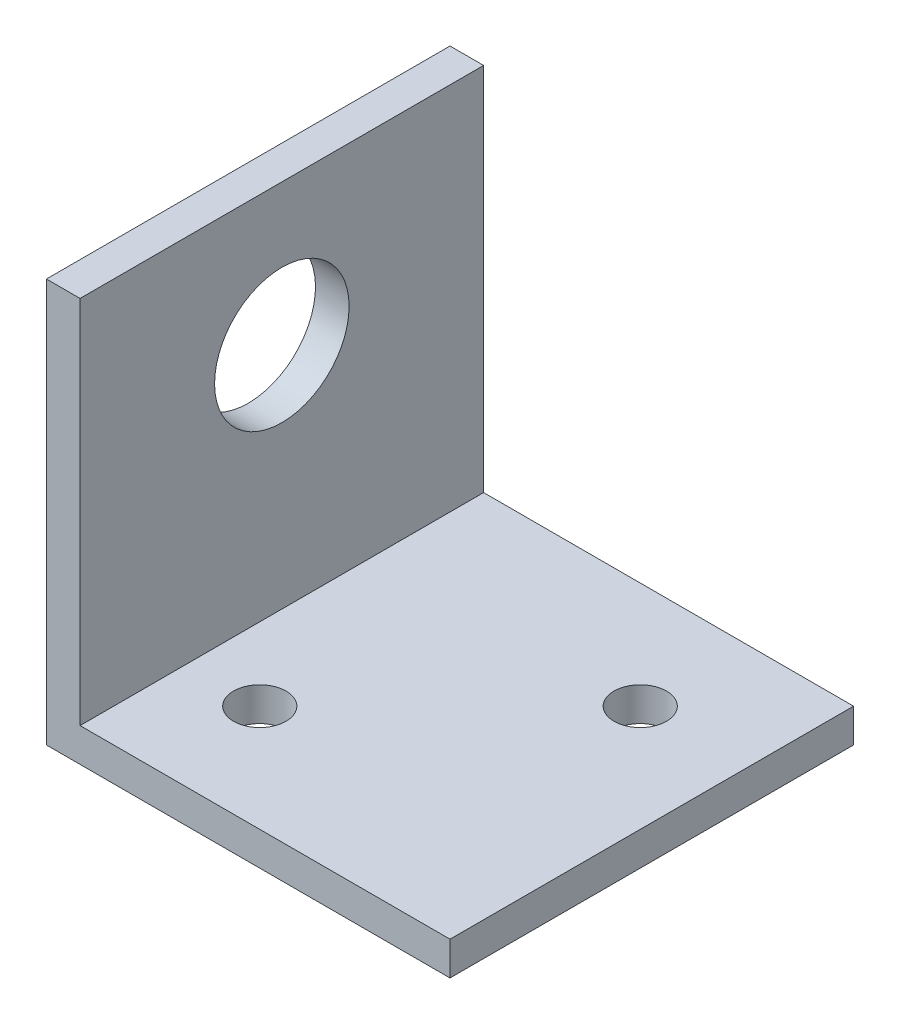
SolidWorks part; units mm, degrees
ref_plane "Front Plane" through (0, 0, 0) normal (0, 0, 1) x (1, 0, 0)
ref_plane "Top Plane" through (0, 0, 0) normal (0, 1, 0) x (1, 0, 0)
ref_plane "Right Plane" through (0, 0, 0) normal (1, 0, 0) x (0, 0, -1)
sketch "Sketch1" plane through (0, 0, 0) normal (0, 0, 1) x (1, 0, 0)
  line L0 (0, 38.1) -> (0, 0)
  line L1 (0, 0) -> (38.1, 0)
  dimension "D1" = 38.1
extrude "Extrude-Thin1" add sketch "Sketch1" along normal blind 38.1 thin thin type one direction reverse wall 3.175
sketch "Sketch2" plane through (0, 0, 0) normal (-1, 0, 0) x (0, 0, 1)
  line L0 (19.05, 0) -> (19.05, 38.1) construction
  line L1 (38.1, 0) -> (0, 0) construction
  line L2 (38.1, 38.1) -> (0, 38.1) construction
  circle A0 centre (19.05, 24.765) radius 6.35
  dimension "D1" = 12.7
  dimension "D2" = 13.335
extrude "Cut-Extrude1" cut sketch "Sketch2" against normal through all
sketch "Sketch3" plane through (0, 0, 0) normal (0, -1, 0) x (1, 0, 0)
  line L0 (38.1, 19.05) -> (0, 19.05) construction
  line L1 (38.1, 38.1) -> (38.1, 0) construction
  line L2 (0, 38.1) -> (0, 0) construction
  line L3 (10.0697, 28.0303) -> (28.0303, 10.0697)
  circle A0 centre (28.0303, 10.0697) radius 2.4765
  circle A1 centre (10.0697, 28.0303) radius 2.4765
  point P9 (19.05, 19.05)
  dimension "D4" = 4.953
  dimension "D1" = 45
  dimension "D2" = 25.4
  dimension "D3" = 19.05
extrude "Cut-Extrude2" cut sketch "Sketch3" against normal through all
